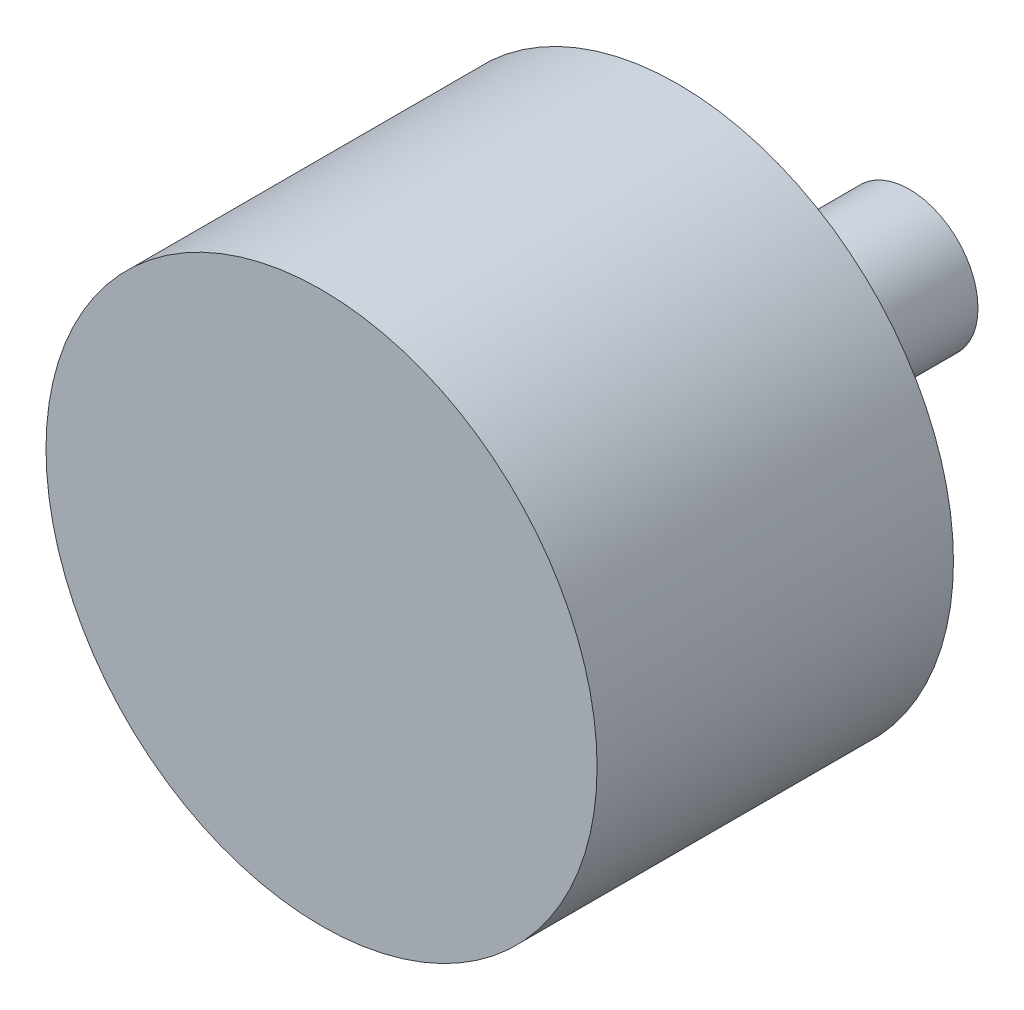
SolidWorks part; units mm, degrees
ref_plane "Front Plane" through (0, 0, 0) normal (0, 0, 1) x (1, 0, 0)
ref_plane "Top Plane" through (0, 0, 0) normal (0, 1, 0) x (1, 0, 0)
ref_plane "Right Plane" through (0, 0, 0) normal (1, 0, 0) x (0, 0, -1)
sketch "Sketch1" plane through (0, 0, 0) normal (1, 0, 0) x (0, 0, -1)
  line L0 (0, 0) -> (0, 19.05)
  line L1 (0, 19.05) -> (24.638, 19.05)
  line L2 (24.638, 19.05) -> (24.638, 5.461)
  line L3 (24.638, 5.461) -> (30.48, 5.461)
  line L4 (30.48, 5.461) -> (30.48, 4.7447)
  line L5 (30.48, 4.7447) -> (40.64, 4.7447)
  line L6 (40.64, 4.7447) -> (40.64, 0)
  line L7 (0, 0) -> (127.5582, 0) construction
  line L8 (0, 0) -> (40.64, 0)
  dimension "D1" = 38.1
  dimension "D2" = 40.64
  dimension "D3" = 24.638
  dimension "D4" = 5.842
  dimension "D5" = 10.922
  dimension "D6" = 9.4894
revolve "Revolve1" add sketch "Sketch1" angle 360 about L7
